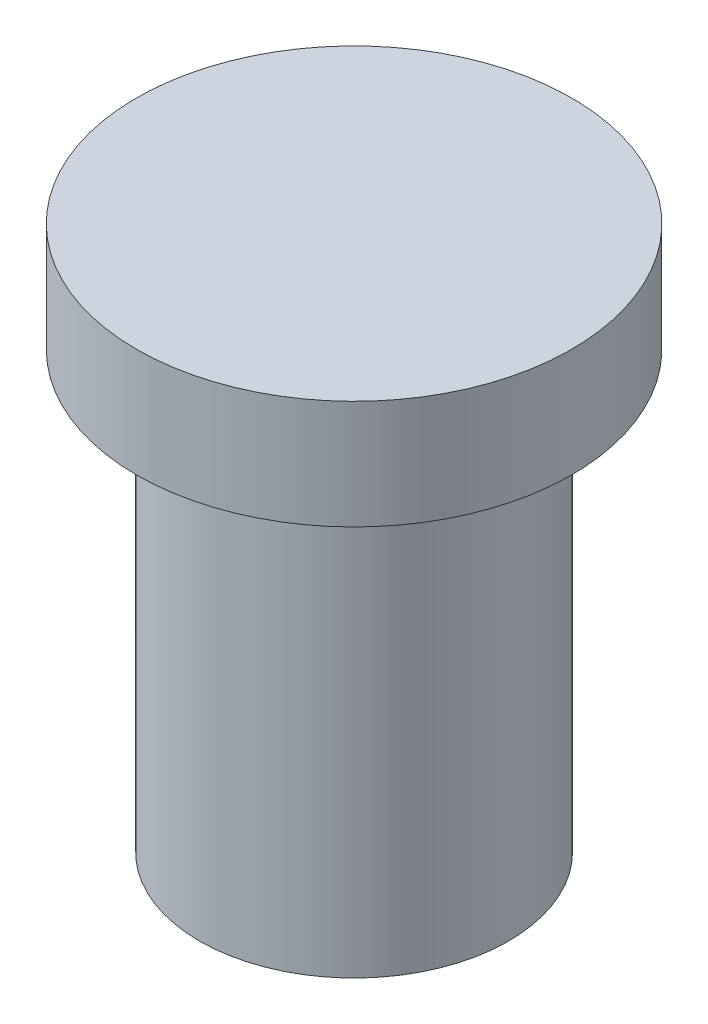
SolidWorks part; units mm, degrees
ref_plane "Front Plane" through (0, 0, 0) normal (0, 0, 1) x (1, 0, 0)
ref_plane "Top Plane" through (0, 0, 0) normal (0, 1, 0) x (1, 0, 0)
ref_plane "Right Plane" through (0, 0, 0) normal (1, 0, 0) x (0, 0, -1)
sketch "Sketch1" plane through (0, 0, 0) normal (0, 1, 0) x (1, 0, 0)
  circle A0 centre (0, 0) radius 3.55
extrude "Boss-Extrude1" add sketch "Sketch1" along normal blind 10
sketch "Sketch2" plane through (0, 10, 0) normal (0, 1, 0) x (1, 0, 0)
  circle A0 centre (0, 0) radius 5
extrude "Boss-Extrude2" add sketch "Sketch2" along normal blind 2.5
